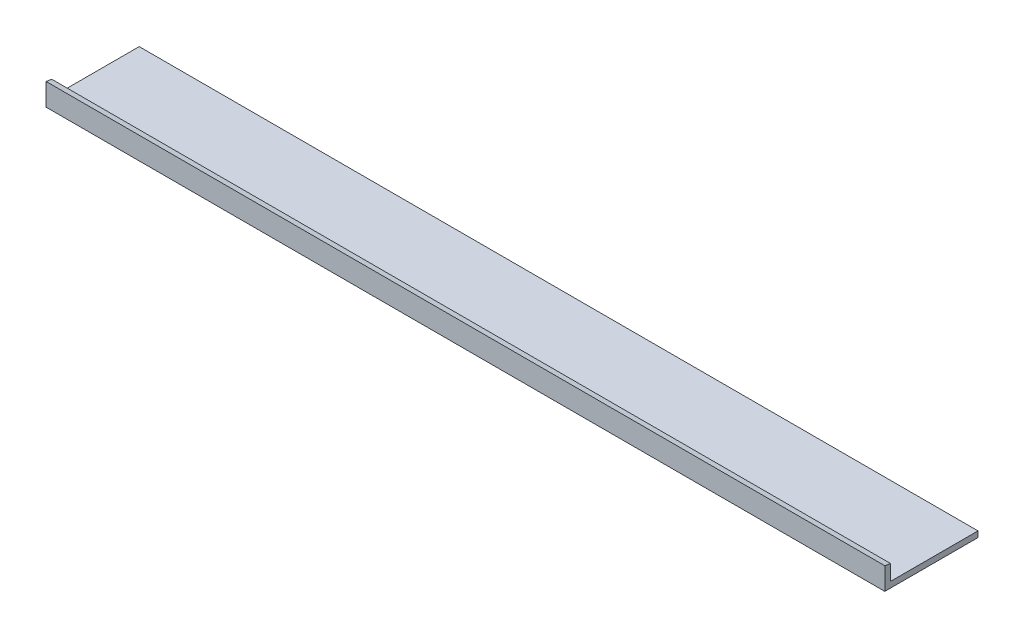
SolidWorks part; units mm, degrees
ref_plane "Front Plane" through (0, 0, 0) normal (0, 0, 1) x (1, 0, 0)
ref_plane "Top Plane" through (0, 0, 0) normal (0, 1, 0) x (1, 0, 0)
ref_plane "Right Plane" through (0, 0, 0) normal (1, 0, 0) x (0, 0, -1)
sketch "Sketch1" plane through (0, 0, 0) normal (1, 0, 0) x (0, 0, -1)
  line L1 (0, 0) -> (50.8, 0)
  line L2 (0, 0) -> (0, 12.1323)
  line L3 (0, 12.1323) -> (50.8, 12.1323)
  line L4 (50.8, 0) -> (50.8, 12.1323)
  dimension "D1" = 12.1323
  dimension "D2" = 50.8
extrude "Boss-Extrude1" add sketch "Sketch1" along normal blind 457.2 contours L2 L1 L4 L3
sketch "Sketch2" plane through (0, 0, 0) normal (-1, 0, 0) x (0, 0, 1)
  line L0 (-41.275, 12.1323) -> (-3.175, 12.1323)
  line L2 (-41.275, 3.175) -> (-3.175, 3.175)
  line L3 (-3.175, 11.5725) -> (-3.175, 3.175)
  line L4 (0, 12.1323) -> (-50.8, 12.1323) construction
  line L5 (-41.275, 3.175) -> (-50.8, 3.175)
  line L6 (-50.8, 0) -> (-50.8, 12.1323) construction
  line L7 (-50.8, 3.175) -> (-50.8, 12.1323)
  line L8 (-41.275, 12.1323) -> (-50.8, 12.1323)
  line L9 (0, 0) -> (-50.8, 0) construction
  line L10 (0, 0) -> (0, 12.1323) construction
  line L11 (-3.175, 12.1323) -> (0, 12.1323)
  line L12 (0, 12.1323) -> (-3.175, 11.5725)
  dimension "D1" = 3.175
  dimension "D2" = 3.175
  dimension "D3" = 10
extrude "Cut-Extrude1" cut sketch "Sketch2" against normal blind 457.2
